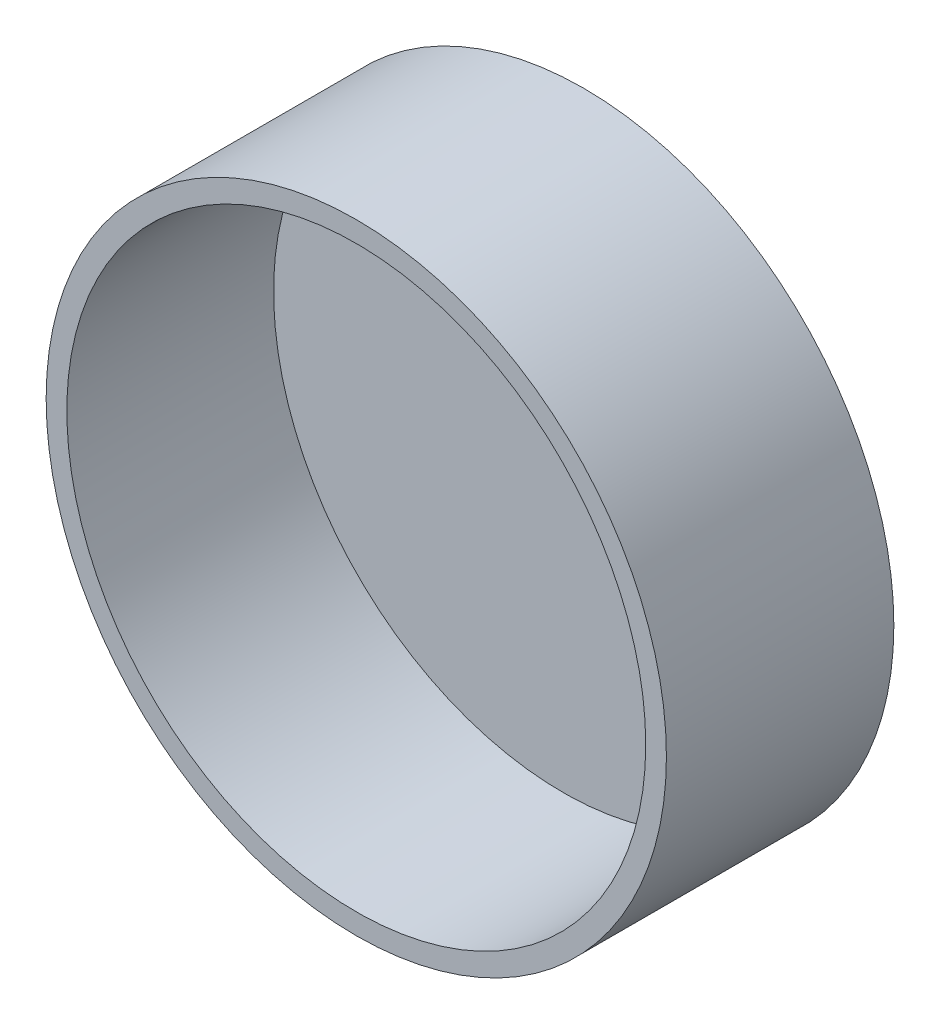
SolidWorks part; units mm, degrees
ref_plane "Front Plane" through (0, 0, 0) normal (0, 0, 1) x (1, 0, 0)
ref_plane "Top Plane" through (0, 0, 0) normal (0, 1, 0) x (1, 0, 0)
ref_plane "Right Plane" through (0, 0, 0) normal (1, 0, 0) x (0, 0, -1)
sketch "Sketch2" plane through (0, 0, 0) normal (0, 0, 1) x (1, 0, 0)
  circle A0 centre (0, 0) radius 15
extrude "Boss-Extrude1" add sketch "Sketch2" along normal blind 11
ref_plane "Plane2" through (0, 0, 11) normal (0, 0, 1) x (1, 0, 0)
sketch "Sketch4" plane through (0, 0, 11) normal (0, 0, 1) x (1, 0, 0)
  circle A0 centre (0, 0) radius 14
extrude "Cut-Extrude1" cut sketch "Sketch4" against normal blind 10
